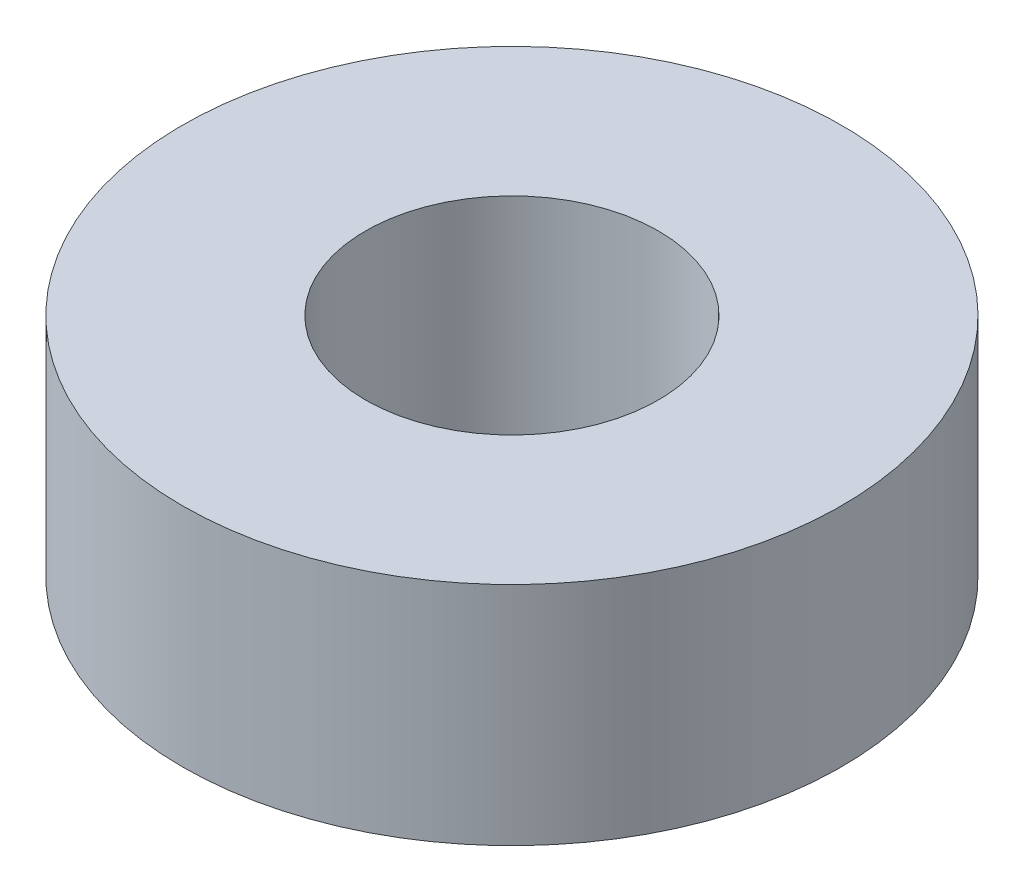
SolidWorks part; units mm, degrees
ref_plane "Front Plane" through (0, 0, 0) normal (0, 0, 1) x (1, 0, 0)
ref_plane "Top Plane" through (0, 0, 0) normal (0, 1, 0) x (1, 0, 0)
ref_plane "Right Plane" through (0, 0, 0) normal (1, 0, 0) x (0, 0, -1)
sketch "Sketch1" plane through (0, 0, 0) normal (0, 1, 0) x (1, 0, 0)
  circle A0 centre (0, 0) radius 7.1438
  circle A1 centre (0, 0) radius 3.175
  dimension "D1" = 6.35
  dimension "D2" = 14.2875
extrude "Extrude1" add sketch "Sketch1" along normal blind 4.9022
